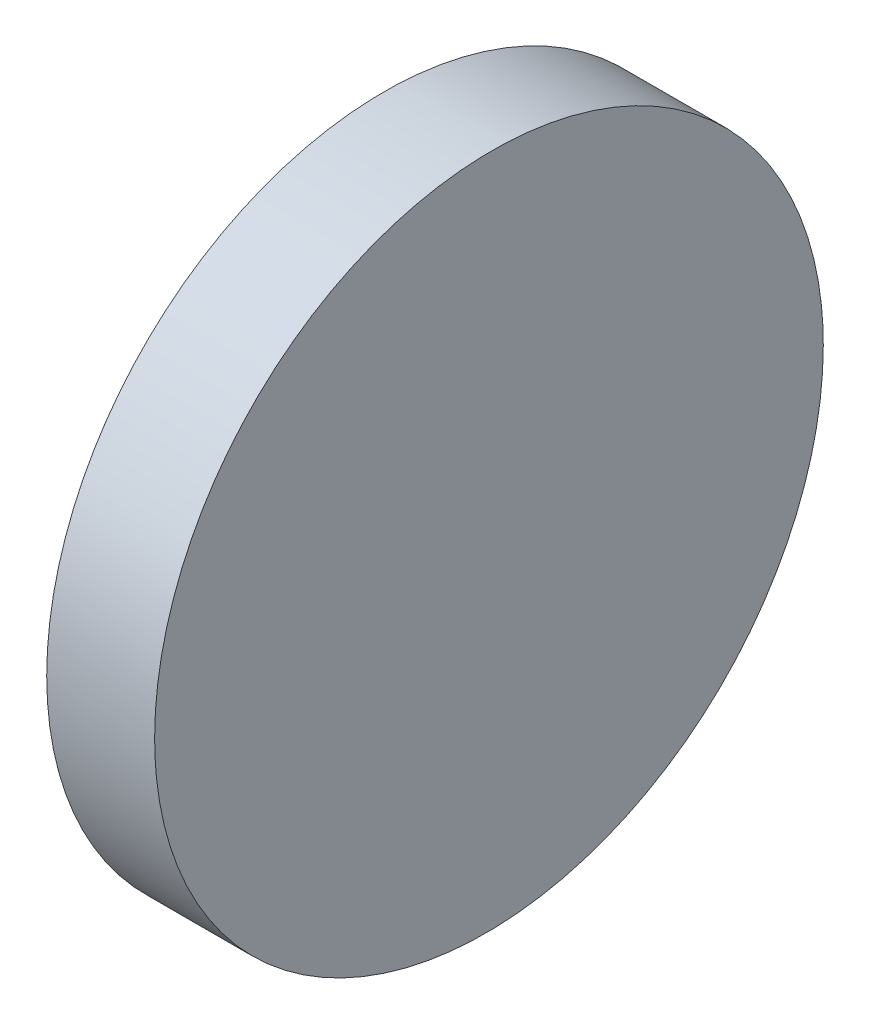
SolidWorks part; units mm, degrees
ref_plane "前视基准面" through (0, 0, 0) normal (0, 0, 1) x (1, 0, 0)
ref_plane "上视基准面" through (0, 0, 0) normal (0, 1, 0) x (1, 0, 0)
ref_plane "右视基准面" through (0, 0, 0) normal (1, 0, 0) x (0, 0, -1)
sketch "草图1" plane through (0, 0, 0) normal (0, 1, 0) x (1, 0, 0)
  line L0 (-12.1202, 0) -> (19.0875, 0) construction
  line L1 (0, 25) -> (0, -25)
  line L2 (0, -25) -> (8, -25)
  line L3 (8, -25) -> (7.5637, 25)
  line L4 (0, 25) -> (7.5637, 25)
  point P5 (0, 0)
  dimension "D1" = 8
  dimension "D2" = 50
  dimension "D3" = 0.5
extrude "凸台-拉伸1" add sketch "草图1" along normal blind 50
sketch "草图5" plane through (0, 0, 0) normal (-1, 0, 0) x (0, 0, 1)
  line L0 (0, 0) -> (0, 50) construction
  line L1 (-25, 50) -> (25, 50) construction
  line L2 (0, 50) -> (0.9302, 12.292) construction
  line L3 (-25, 25) -> (25, 25) construction
  line L4 (-25, 50) -> (-25, 0) construction
  line L5 (25, 50) -> (25, 0) construction
  line L6 (25, 25) -> (6.6453, 6.1075) construction
  line L11 (-25, 0) -> (25, 0)
  line L12 (25, 0) -> (25, 50)
  line L13 (25, 50) -> (-25, 50)
  line L14 (-25, 50) -> (-25, 0)
  line L15 (-25, 0) -> (25, 0)
  line L16 (25, 0) -> (25, 50)
  line L17 (25, 50) -> (-25, 50)
  line L18 (-25, 50) -> (-25, 0)
  circle A0 centre (0, 25) radius 25
  line M5 (-25, 0) -> (25, 0)
  line M6 (25, 0) -> (25, 50)
  line M7 (25, 50) -> (-25, 50)
  line M8 (-25, 50) -> (-25, 0)
  dimension "D1" = 50
  dimension "D2" = 0
extrude "切除-拉伸2" cut sketch "草图5" against normal blind 12.5 contours A0 L17 M8 | A0 L18 M5 | A0 L15 M6 | A0 L16 M7
